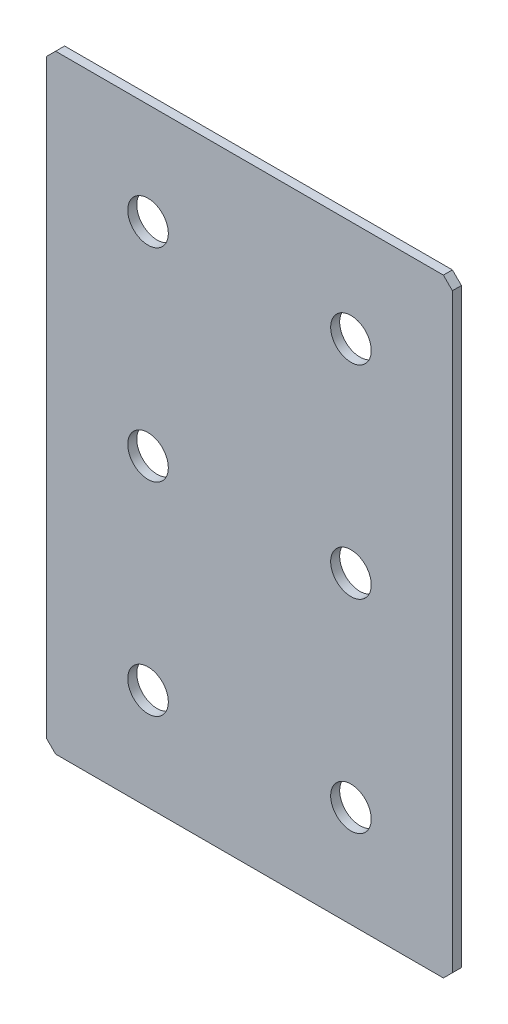
SolidWorks part; units mm, degrees
material "Простая углеродистая сталь"
ref_plane "Спереди(Плоскость XY)" through (0, 0, 0) normal (0, 0, 1) x (1, 0, 0)
ref_plane "Сверху(Плоскость XZ)" through (0, 0, 0) normal (0, 1, 0) x (1, 0, 0)
ref_plane "Справа(Плоскость ZY)" through (0, 0, 0) normal (1, 0, 0) x (0, 0, -1)
sketch "Эскиз1" plane through (0, 0, 0) normal (0, 0, 1) x (1, 0, 0)
  line L1 (-45, -67.5) -> (45, -67.5)
  line L2 (-45, -67.5) -> (-45, 67.5)
  line L3 (-45, 67.5) -> (45, 67.5)
  line L4 (45, -67.5) -> (45, 67.5)
  line L5 (-45, -67.5) -> (45, 67.5) construction
  line L6 (-45, 67.5) -> (45, -67.5) construction
  point P0 (0, 0)
  dimension "D1" = 90
  dimension "D2" = 135
extrude "Бобышка-Вытянуть1" add sketch "Эскиз1" along normal blind 2
chamfer "Фаска1" distance 2 angle 45 4 edges at (-45, -67.5, 1) (45, -67.5, 1) (-45, 67.5, 1) (45, 67.5, 1)
hole_wizard "Отверстие с зазором M81" positions "Эскиз2" profile "Эскиз3" hole size "M8" standard "DIN" end condition through all
sketch "Эскиз2" plane through (0, 0, 2) normal (0, 0, 1) x (1, 0, 0)
  line L0 (-22.5, 0) -> (22.5, 0) construction
  line L1 (22.5, 0) -> (22.5, 45) construction
  line L3 (22.5, 0) -> (22.5, -45) construction
  line L5 (-22.5, 0) -> (-22.5, 45) construction
  line L7 (-22.5, 0) -> (-22.5, -45) construction
  point P0 (-22.5, 45)
  point P2 (22.5, 45)
  point P4 (22.5, 0)
  point P6 (-22.5, 0)
  point P8 (-22.5, -45)
  point P10 (22.5, -45)
  dimension "D1" = 45
sketch "Эскиз3" plane through (-22.5, 45, 2) normal (1, 0, 0) x (0, -1, 0)
  line L0 (0, 0) -> (0, 2)
  line L1 (0, 2) -> (4.5, 2)
  line L2 (4.5, 2) -> (4.5, 0)
  line L5 (4.5, 0) -> (0, 0)
  line L11 (0, -6.35) -> (0, 107.95) construction
  dimension "Диаметр сквозного отверстия" = 9
  dimension "Глубина сквозного отверстия" = 2
